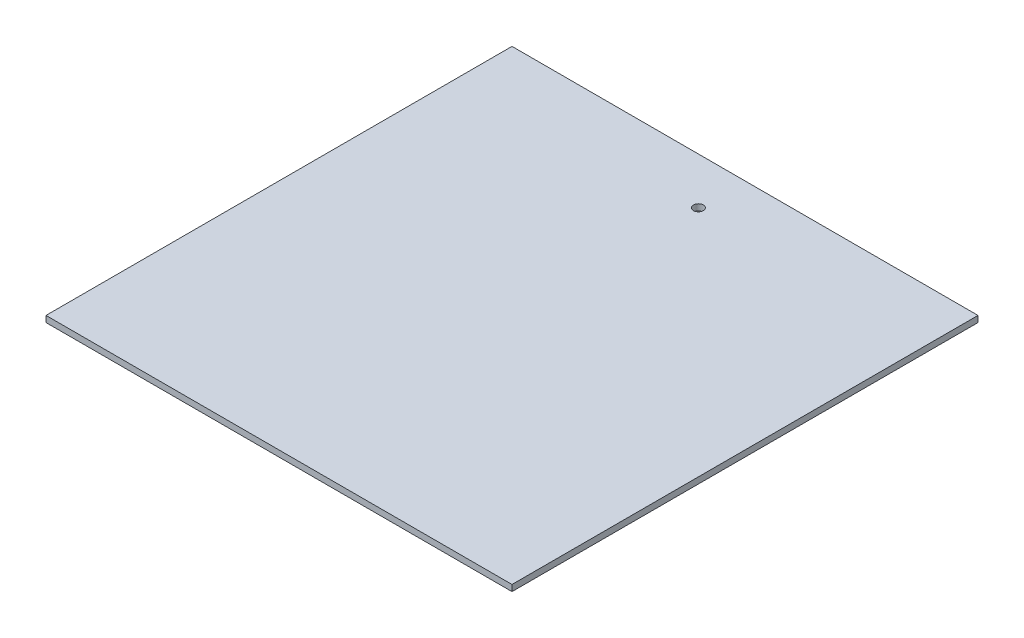
SolidWorks part; units mm, degrees
ref_plane "Front Plane" through (0, 0, 0) normal (0, 0, 1) x (1, 0, 0)
ref_plane "Top Plane" through (0, 0, 0) normal (0, 1, 0) x (1, 0, 0)
ref_plane "Right Plane" through (0, 0, 0) normal (1, 0, 0) x (0, 0, -1)
sketch "Sketch1" plane through (0, 0, 0) normal (0, 1, 0) x (1, 0, 0)
  line L1 (-95.25, -95.25) -> (95.25, -95.25)
  line L2 (-95.25, -95.25) -> (-95.25, 95.25)
  line L3 (-95.25, 95.25) -> (95.25, 95.25)
  line L4 (95.25, -95.25) -> (95.25, 95.25)
  line L5 (-95.25, -95.25) -> (95.25, 95.25) construction
  line L6 (-95.25, 95.25) -> (95.25, -95.25) construction
  point P0 (0, 0)
  dimension "D1" = 190.5
  dimension "D2" = 190.5
extrude "Boss-Extrude1" add sketch "Sketch1" along normal blind 2.54
sketch "Sketch2" plane through (0, 2.54, 0) normal (0, 1, 0) x (1, 0, 0)
  circle A0 centre (0.0008, 76.1992) radius 2.032
extrude "Cut-Extrude1" cut sketch "Sketch2" against normal up to surface (2.54 mm away) up to face at (0, 0, 0)
